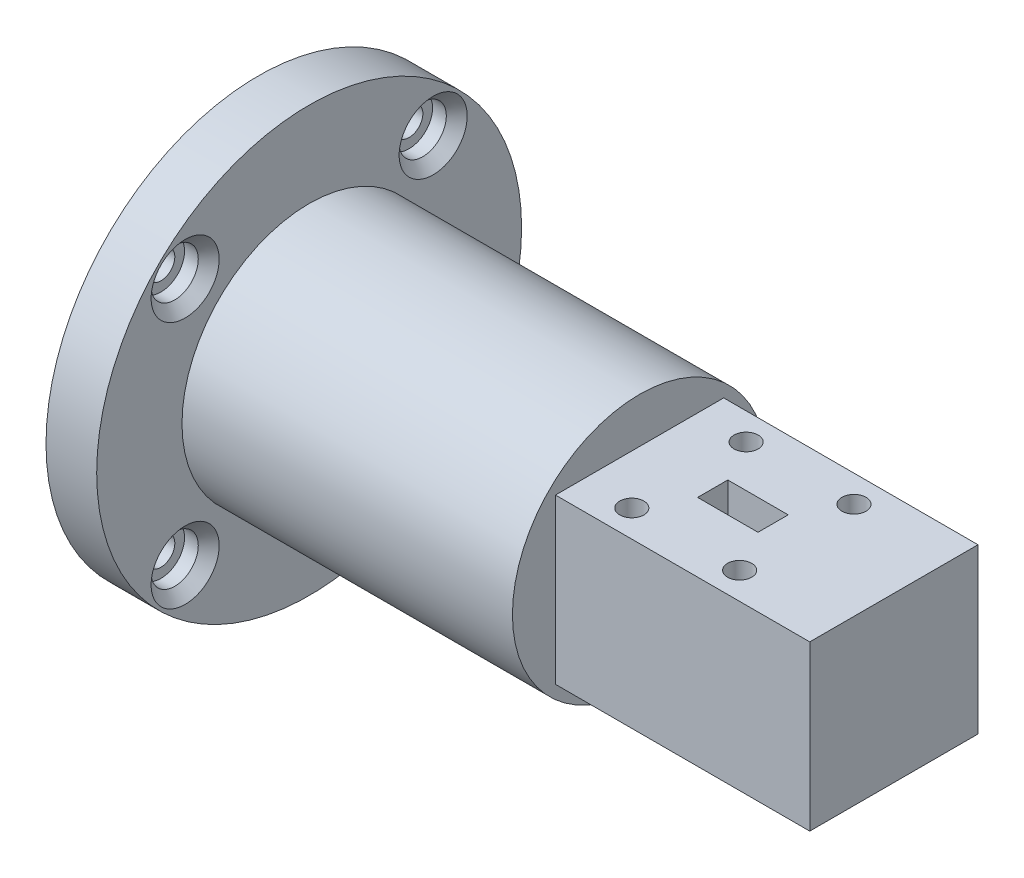
SolidWorks part; units mm, degrees
ref_plane "Front Plane" through (0, 0, 0) normal (0, 0, 1) x (1, 0, 0)
ref_plane "Top Plane" through (0, 0, 0) normal (0, 1, 0) x (1, 0, 0)
ref_plane "Right Plane" through (0, 0, 0) normal (1, 0, 0) x (0, 0, -1)
sketch "Sketch1" plane through (0, 0, 0) normal (1, 0, 0) x (0, 0, -1)
  circle A0 centre (0, 0) radius 25.019
  dimension "D1" = 50.038
extrude "Boss-Extrude1" add sketch "Sketch1" along normal blind 5.969
sketch "Sketch2" plane through (5.969, 0, 0) normal (1, 0, 0) x (0, 0, -1)
  circle A0 centre (0, 0) radius 14.9733
  dimension "D1" = 29.9466
extrude "Boss-Extrude2" add sketch "Sketch2" along normal blind 38.9128
sketch "Sketch3" plane through (44.8818, 0, 0) normal (1, 0, 0) x (0, 0, -1)
  line L0 (0, 10.4765) -> (0, -12.5019) construction
  line L1 (-9.906, -9.652) -> (9.906, -9.652)
  line L2 (-9.906, -9.652) -> (-9.906, 9.652)
  line L3 (-9.906, 9.652) -> (9.906, 9.652)
  line L4 (9.906, -9.652) -> (9.906, 9.652)
  line L5 (-12.7781, 0) -> (12.4098, 0) construction
  dimension "D1" = 19.304
  dimension "D2" = 19.812
extrude "Boss-Extrude3" add sketch "Sketch3" along normal blind 29.9466
hole_wizard "CBORE for #4 Socket Head Cap Screw1" positions "Sketch5" profile "Sketch4" counterbore size "#4" standard "ANSI Inch" end condition through all
sketch "Sketch5" plane through (5.969, 0, 0) normal (1, 0, 0) x (0, 0, -1)
  line L0 (0, 0) -> (-17.6911, 17.6911) construction
  line L1 (0, 0) -> (17.6911, 17.6911) construction
  line L2 (0, 0) -> (-17.6911, -17.6911) construction
  line L3 (0, 0) -> (17.6911, -17.6911) construction
  line L4 (0, 0) -> (0, 25.019) construction
  circle A0 centre (0, 0) radius 25.019 construction
  point P0 (14.605, 14.605)
  point P2 (-14.605, 14.605)
  point P4 (14.605, -14.605)
  point P6 (-14.605, -14.605)
  dimension "D1" = 90
  dimension "D2" = 45
  dimension "D3" = 29.21
sketch "Sketch4" plane through (5.969, 14.605, -14.605) normal (0, 1, 0) x (0, 0, -1)
  line L0 (0, 0) -> (0, 5.969)
  line L1 (0, 5.969) -> (1.6319, 5.969)
  line L3 (1.6319, 5.969) -> (1.6319, 2.8448)
  line L4 (2.7788, 2.8448) -> (1.6319, 2.8448)
  line L5 (2.7788, 2.8448) -> (2.7788, 1.2294)
  line L6 (2.7788, 1.2294) -> (4.0081, 0)
  line L7 (4.0081, 0) -> (0, 0)
  line L8 (-2.7788, 1.2294) -> (-4.0081, 0) construction
  line L11 (0, -6.35) -> (0, 107.95) construction
  dimension "Thru Hole Dia." = 3.2639
  dimension "Thru Hole Depth" = 5.969
  dimension "C'Bore Dia." = 5.5575
  dimension "C'Bore Depth" = 2.8448
  dimension "Near C'Sink Dia." = 8.0162
  dimension "Near C'Sink Angle" = 90
sketch "Sketch6" plane through (0, 9.652, 0) normal (0, 1, 0) x (1, 0, 0)
  line L0 (57.0484, 9.906) -> (57.0484, -9.906) construction
  line L1 (53.4924, -1.778) -> (60.6044, -1.778)
  line L2 (53.4924, -1.778) -> (53.4924, 1.778)
  line L3 (53.4924, 1.778) -> (60.6044, 1.778)
  line L4 (60.6044, -1.778) -> (60.6044, 1.778)
  line L5 (49.8822, 0) -> (66.3076, 0) construction
  line L6 (74.8284, -9.906) -> (44.8818, -9.906) construction
  line L7 (74.8284, 9.906) -> (44.8818, 9.906) construction
  line L9 (74.8284, 9.906) -> (74.8284, -9.906) construction
  circle A0 centre (63.3984, 6.731) radius 1.4224
  circle A1 centre (50.6984, 6.731) radius 1.4224
  circle A2 centre (50.6984, -6.731) radius 1.4224
  circle A3 centre (63.3984, -6.731) radius 1.4224
  dimension "D3" = 2.8448
  dimension "D1" = 7.112
  dimension "D2" = 3.556
  dimension "D4" = 6.731
  dimension "D5" = 6.35
  dimension "D6" = 6.35
  dimension "D7" = 6.731
  dimension "D8" = 6.731
  dimension "D9" = 11.43
extrude "Cut-Extrude1" cut sketch "Sketch6" against normal blind 5.08
sketch "Sketch7" plane through (0, 0, -9.906) normal (0, 0, -1) x (-1, 0, 0)
  line L0 (-65.3034, -8.1382) -> (-65.3034, 7.1808) construction
  line L1 (-68.8594, 1.778) -> (-61.7474, 1.778)
  line L2 (-68.8594, 1.778) -> (-68.8594, -1.778)
  line L3 (-68.8594, -1.778) -> (-61.7474, -1.778)
  line L4 (-61.7474, 1.778) -> (-61.7474, -1.778)
  line L5 (-68.6551, 0) -> (-48.4425, 0) construction
  line L6 (-74.8284, -9.652) -> (-74.8284, 9.652) construction
  circle A0 centre (-71.6534, 6.731) radius 1.4224
  circle A1 centre (-58.9534, 6.731) radius 1.4224
  circle A2 centre (-58.9534, -6.731) radius 1.4224
  circle A3 centre (-71.6534, -6.731) radius 1.4224
  dimension "D3" = 2.8448
  dimension "D1" = 7.112
  dimension "D2" = 3.556
  dimension "D4" = 6.731
  dimension "D5" = 6.731
  dimension "D6" = 6.35
  dimension "D7" = 6.35
  dimension "D8" = 3.175
extrude "Cut-Extrude2" cut sketch "Sketch7" against normal blind 5.08
sketch "Sketch8" plane through (0, 0, 0) normal (-1, 0, 0) x (0, 0, 1)
  circle A0 centre (0, 0) radius 4.7308
  dimension "D1" = 9.4615
extrude "Cut-Extrude3" cut sketch "Sketch8" against normal blind 12.7
